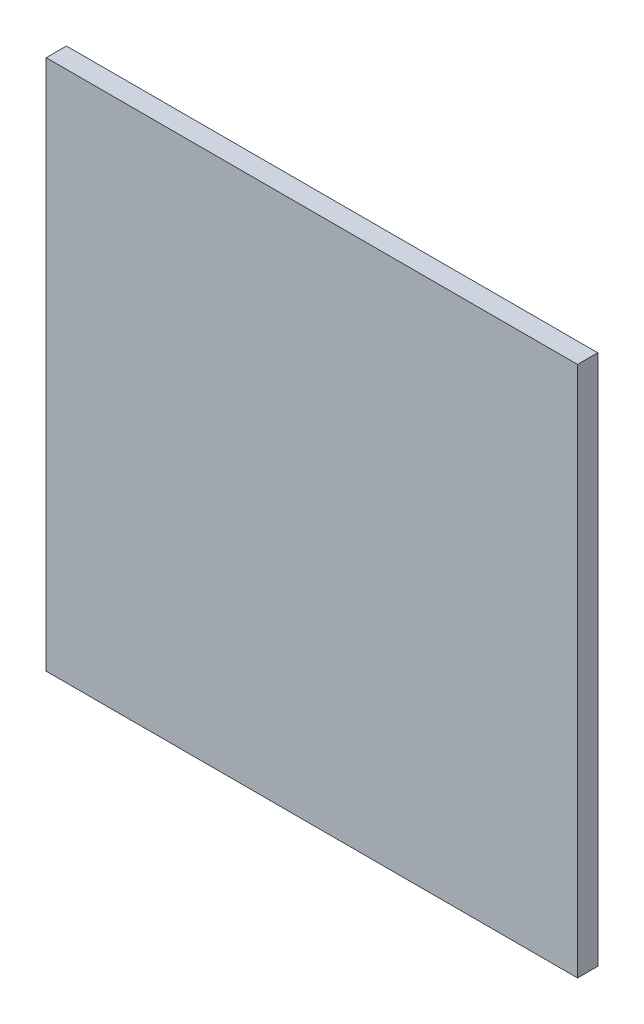
SolidWorks part; units mm, degrees
ref_plane "前视基准面" through (0, 0, 0) normal (0, 0, 1) x (1, 0, 0)
ref_plane "上视基准面" through (0, 0, 0) normal (0, 1, 0) x (1, 0, 0)
ref_plane "右视基准面" through (0, 0, 0) normal (1, 0, 0) x (0, 0, -1)
other "Configuration Table"
sketch "Sketch1" plane through (0, 0, 0) normal (0, 0, 1) x (1, 0, 0)
  line L1 (0, 0) -> (105, 0)
  line L2 (0, 0) -> (0, 105)
  line L3 (0, 105) -> (105, 105)
  line L4 (105, 0) -> (105, 105)
  dimension "D1" = 105
  dimension "D2" = 105
extrude "Boss-Extrude1" add sketch "Sketch1" along normal blind 4
sketch "Sketch2" plane through (0, 0, 0) normal (0, 0, -1) x (-1, 0, 0)
  line L0 (0, 0) -> (-105, 0) construction
  line L1 (-105, 0) -> (-105, 105) construction
  circle A0 centre (-52.5, 52.5) radius 3
  dimension "D2" = 52.5
  dimension "D3" = 6
  dimension "D1" = 52.5
extrude "Cut-Extrude1" cut sketch "Sketch2" against normal blind 2
sketch "Sketch3" plane through (0, 0, 0) normal (0, 0, -1) x (-1, 0, 0)
  line L0 (0, 105) -> (0, 0) construction
  line L1 (-105, 105) -> (0, 105) construction
  line L3 (-46.5, 55) -> (-40, 55)
  line L5 (-49.4406, 53) -> (-40, 53)
  line L6 (-40, 55) -> (-40, 53)
  line L7 (-46.5, 50) -> (-40, 50)
  line L9 (-49.4406, 52) -> (-40, 52)
  line L10 (-40, 50) -> (-40, 52)
  arc A1 (-49.4406, 53) -> (-49.4406, 52) centre (-52.5, 52.5) ccw
  arc A2 (-46.5, 55) -> (-46.5, 50) centre (-52.5, 52.5) ccw
  point P4 (-42, 50)
  point P5 (-42, 50)
  point P9 (-42, 50)
  point P11 (-40.8343, 52)
  dimension "D1" = 13
  dimension "D2" = 6.2
  dimension "D3" = 52.5
  dimension "D4" = 52.5
  dimension "D5" = 1
  dimension "D6" = 2
  dimension "D7" = 40
  dimension "D8" = 40
  dimension "D9" = 46.5
  dimension "D10" = 46.5
  dimension "D11" = 55
extrude "Boss-Extrude5" add sketch "Sketch3" along normal blind 12
sketch "Sketch4" plane through (0, 55, 0) normal (0, 1, 0) x (1, 0, 0)
  line L0 (40, 12) -> (46.5, 12) construction
  line L1 (40, 12) -> (40, 0) construction
  circle A0 centre (43.25, 6) radius 1.9987
  point P4 (43.25, 12)
  point P5 (0, 0)
  point P8 (40, 6)
  dimension "D1" = 3.9974
extrude "Cut-Extrude2" cut sketch "Sketch4" against normal blind 12
fillet "Fillet1" radius 1 2 edges at (40, 51, -12) (40, 54, -12)
